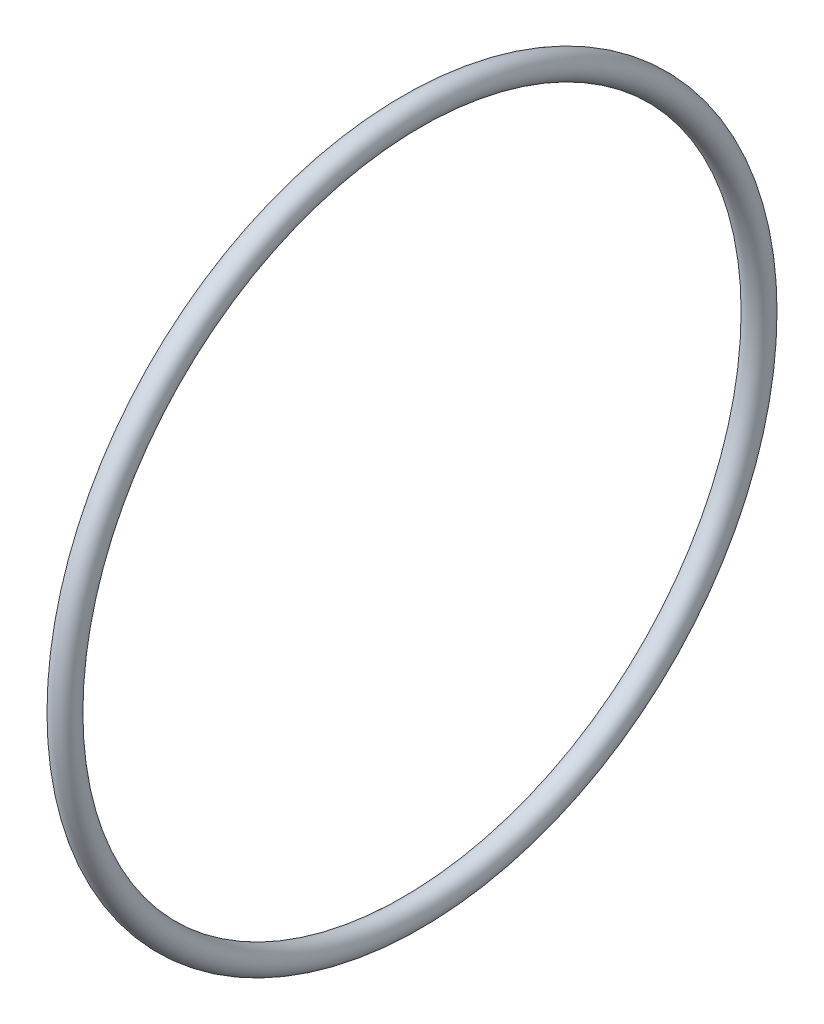
SolidWorks part; units mm, degrees
ref_plane "Front Plane" through (0, 0, 0) normal (0, 0, 1) x (1, 0, 0)
ref_plane "Top Plane" through (0, 0, 0) normal (0, 1, 0) x (1, 0, 0)
ref_plane "Right Plane" through (0, 0, 0) normal (1, 0, 0) x (0, 0, -1)
sketch "Sketch2" plane through (0, 0, 0) normal (0, 0, 1) x (1, 0, 0)
  line L0 (0, 0) -> (58.591, 0) construction
  line L2 (0, 0) -> (18.4, 0)
  line L3 (0, 0) -> (0, 2.5)
  line L4 (0, 2.5) -> (18.4, 2.5)
  line L5 (18.4, 0) -> (18.4, 2.5)
  line L6 (6.0094, 2.5) -> (6.0094, 6)
  line L11 (6.0094, 6) -> (9.9794, 6)
  line L16 (12.9794, 6) -> (12.9794, 3)
  line L17 (12.9794, 3) -> (13.6398, 3)
  line L18 (13.6398, 3) -> (13.6398, 2.5)
  line L19 (13.6398, 2.5) -> (6.0094, 2.5)
  line L22 (13.6398, 2.5) -> (16.1198, 2.5)
  line L23 (13.6398, 2.5) -> (13.6398, 4)
  line L24 (13.6398, 4) -> (16.1198, 4)
  line L25 (16.1198, 2.5) -> (16.1198, 4)
  line L27 (6.0094, 6) -> (9.9794, 6)
  line L28 (6.0094, 6) -> (6.0094, 9)
  line L29 (6.0094, 9) -> (9.9794, 9)
  line L30 (9.9794, 6) -> (9.9794, 9)
  line L31 (6.0094, 9) -> (6.0094, 8.25)
  line L32 (6.0094, 8.25) -> (5.0094, 8.25)
  line L33 (8.6609, 22.001) -> (8.6609, 12.476) construction
  line L34 (5.0094, 12.476) -> (12.3124, 12.476)
  line L35 (9.9794, 9) -> (12.3124, 9)
  line L36 (5.0094, 7.9375) -> (1.7709, 7.9375)
  line L37 (5.0094, 8.25) -> (5.0094, 12.476)
  line L38 (5.0094, 7.9375) -> (5.0094, 13.9365)
  line L39 (5.0094, 13.9365) -> (1.7709, 13.9365)
  line L40 (1.7709, 7.9375) -> (1.7709, 13.9365)
  line L41 (5.0094, 22.001) -> (12.3124, 22.001)
  line L42 (5.0094, 22.001) -> (5.0094, 30.1625)
  line L43 (5.0094, 30.1625) -> (12.3124, 30.1625)
  line L44 (12.3124, 22.001) -> (12.3124, 30.1625)
  line L49 (16.6398, 22.001) -> (16.6398, 7.5)
  line L51 (23.0198, 7.5) -> (23.0198, 6.5)
  line L54 (16.1198, 4) -> (13.6398, 4)
  line L56 (18.0398, 7.5) -> (23.0198, 7.5)
  line L57 (13.3124, 22.001) -> (16.6398, 22.001)
  line L58 (16.1198, 3.5) -> (20.0198, 3.5)
  line L59 (29.9098, 14) -> (26.9098, 11)
  line L60 (4.0094, 31.75) -> (18.0398, 31.75)
  line L61 (18.0398, 7.5) -> (23.0198, 7.5)
  line L62 (18.0398, 7.5) -> (18.0398, 12)
  line L63 (18.0398, 12) -> (23.0198, 12)
  line L64 (23.0198, 7.5) -> (23.0198, 12)
  line L65 (18.0398, 31.75) -> (18.0398, 12)
  line L66 (23.0198, 11) -> (26.9098, 11)
  line L67 (34.8098, 23) -> (31.3098, 19.5)
  line L68 (35.8098, 31) -> (38.7998, 33.99)
  line L69 (29.9098, 14) -> (29.9098, 15)
  line L70 (29.9098, 15) -> (22.9398, 15)
  line L71 (22.9398, 15) -> (21.0398, 15)
  line L72 (18.0398, 7.5) -> (16.6398, 7.5)
  line L73 (21.0398, 15) -> (21.0398, 43)
  line L74 (19.6115, 40) -> (9.6516, 40)
  line L75 (9.6516, 40) -> (4.0094, 40)
  line L76 (21.0398, 43) -> (19.6115, 43)
  line L77 (22.9398, 15) -> (29.9098, 15)
  line L78 (22.9398, 15) -> (22.9398, 21)
  line L79 (22.9398, 21) -> (29.9098, 21)
  line L80 (29.9098, 15) -> (29.9098, 21)
  line L81 (9.6516, 40) -> (19.6115, 40)
  line L82 (9.6516, 40) -> (9.6516, 50)
  line L83 (9.6516, 50) -> (19.6115, 50)
  line L84 (19.6115, 40) -> (19.6115, 50)
  line L85 (4.0094, 40) -> (4.0094, 31.75)
  line L86 (12.9794, 3) -> (12.9794, 2.5)
  line L87 (31.3098, 19.5) -> (29.9098, 19.5)
  line L88 (21.4694, 63.5) -> (21.4694, 51.308)
  line L89 (21.4694, 63.5) -> (25.9398, 63.5)
  line L90 (25.9398, 63.5) -> (25.9398, 25)
  line L91 (27.8398, 25) -> (25.9398, 25)
  line L92 (9.6516, 48) -> (8.2233, 48)
  line L93 (8.2233, 48) -> (8.2233, 53.476)
  line L94 (8.2233, 53.476) -> (19.6115, 53.476)
  line L95 (19.6115, 53.476) -> (19.6115, 50)
  line L96 (13.9174, 63.001) -> (13.9174, 53.476) construction
  line L97 (8.2233, 63.001) -> (19.6115, 63.001)
  line L98 (8.2233, 63.001) -> (8.2233, 68.2625)
  line L99 (8.2233, 68.2625) -> (19.6115, 68.2625)
  line L100 (19.6115, 63.001) -> (19.6115, 68.2625)
  line L101 (12.9794, 6) -> (11.9794, 6)
  line L102 (8.2233, 44.825) -> (4.9848, 44.825)
  line L103 (8.2233, 44.825) -> (8.2233, 54.9365)
  line L104 (8.2233, 54.9365) -> (4.9848, 54.9365)
  line L106 (9.9794, 6) -> (10.8794, 6)
  line L107 (27.8398, 25) -> (34.8098, 25)
  line L108 (34.8098, 25) -> (34.8098, 23)
  line L109 (0, 0) -> (-2, 0)
  line L110 (0, 0) -> (0, 11)
  line L111 (27.8398, 25) -> (34.8098, 25)
  line L112 (27.8398, 25) -> (27.8398, 32.5)
  line L113 (27.8398, 32.5) -> (34.8098, 32.5)
  line L114 (34.8098, 25) -> (34.8098, 32.5)
  line L115 (35.8098, 31) -> (34.8098, 31)
  line L116 (27.8398, 32.5) -> (27.8398, 64.5)
  line L117 (20.5849, 74.025) -> (6.2499, 74.025)
  line L118 (6.2499, 74.025) -> (6.2499, 76.2)
  line L119 (38.7998, 47.29) -> (30.8398, 55.25)
  line L120 (0, 11) -> (-2, 11)
  line L121 (38.7998, 43.815) -> (30.8623, 43.815)
  line L123 (-4.8152, 69.85) -> (1.5348, 76.2)
  line L124 (38.7998, 47.29) -> (38.7998, 33.99)
  line L125 (-2, 0) -> (-2, 11)
  line L126 (38.7998, 37.465) -> (30.8623, 37.465)
  line L127 (30.8623, 43.815) -> (30.8623, 37.465)
  line L128 (6.0094, 2.5) -> (6.0094, 0)
  line L129 (-0.0152, 63.5) -> (-0.0152, 30)
  line L132 (4.9848, 63.5) -> (-0.0152, 63.5)
  line L136 (-1.8152, 30) -> (-11.7752, 30)
  line L138 (-13.7752, 25.4) -> (-2, 25.4)
  line L139 (-2, 25.4) -> (-2, 11.5)
  line L140 (27.8398, 64.5) -> (20.5849, 64.5)
  line L141 (-1.8152, 30) -> (-11.7752, 30)
  line L142 (-1.8152, 30) -> (-1.8152, 39)
  line L143 (-1.8152, 39) -> (-11.7752, 39)
  line L144 (-11.7752, 30) -> (-11.7752, 39)
  line L145 (20.5849, 64.5) -> (20.5849, 74.025)
  line L146 (-12.7752, 37) -> (-12.7752, 47.29)
  line L147 (-12.7752, 37) -> (-11.7752, 37)
  line L148 (30.8398, 55.25) -> (30.8398, 76.2)
  line L149 (11.9794, 6) -> (11.9794, 5.45)
  line L154 (-2, 11.5) -> (0.5, 11.5)
  line L155 (4.9848, 60.6197) -> (24.0348, 60.6197)
  line L160 (4.9848, 60.6197) -> (4.9848, 55.8572)
  line L161 (4.9848, 55.8572) -> (24.0348, 55.8572)
  line L166 (24.0348, 60.6197) -> (24.0348, 55.8572)
  line L167 (4.9848, 60.6197) -> (24.0348, 55.8572) construction
  line L172 (4.9848, 55.8572) -> (24.0348, 60.6197) construction
  line L173 (24.0348, 62.2072) -> (25.9398, 62.2072)
  line L174 (11.9794, 5.45) -> (10.8794, 5.45)
  line L175 (10.8794, 6) -> (10.8794, 5.45)
  line L176 (24.0348, 62.2072) -> (24.0348, 54.2697)
  line L177 (24.0348, 54.2697) -> (25.9398, 54.2697)
  line L178 (25.9398, 62.2072) -> (25.9398, 54.2697)
  line L179 (24.0348, 62.2072) -> (25.9398, 54.2697) construction
  line L180 (24.0348, 54.2697) -> (25.9398, 62.2072) construction
  line L181 (3, 19.6197) -> (15.7, 19.6197)
  line L182 (3, 19.6197) -> (3, 14.8572)
  line L183 (3, 14.8572) -> (15.7, 14.8572)
  line L184 (15.7, 19.6197) -> (15.7, 14.8572)
  line L185 (3, 19.6197) -> (15.7, 14.8572) construction
  line L186 (3, 14.8572) -> (15.7, 19.6197) construction
  line L187 (15.7, 21.2072) -> (16.6398, 21.2072)
  line L188 (15.7, 21.2072) -> (15.7, 13.2697)
  line L189 (15.7, 13.2697) -> (16.6398, 13.2697)
  line L190 (16.6398, 21.2072) -> (16.6398, 13.2697)
  line L191 (15.7, 21.2072) -> (16.6398, 13.2697) construction
  line L192 (15.7, 13.2697) -> (16.6398, 21.2072) construction
  line L193 (0.5, 11.5) -> (0.5, 6.9375)
  line L194 (0.5, 6.9375) -> (1.7709, 6.9375)
  line L195 (23.0198, 6.5) -> (20.0198, 3.5)
  line L196 (4.9848, 63.5) -> (4.9848, 54.9365)
  line L197 (3, 43.825) -> (4.9848, 43.825)
  line L198 (1.7709, 6.9375) -> (1.7709, 7.9375)
  line L199 (6.0094, 0) -> (12.9794, 0)
  line L200 (12.9794, 0) -> (12.9794, 2.5)
  line L201 (18.0398, 31.75) -> (18.0398, 35.875)
  line L202 (18.0398, 35.875) -> (21.0398, 35.875)
  line L203 (30.8398, 76.2) -> (6.2499, 76.2)
  line L204 (2.8049, 69.85) -> (7.2499, 69.85) construction
  line L205 (7.2499, 67.4688) -> (26.2999, 67.4688)
  line L206 (7.2499, 74.025) -> (7.2499, 64.5)
  line L207 (7.2499, 64.5) -> (-1.8152, 64.5)
  line L208 (-1.8152, 64.5) -> (-1.8152, 39)
  line L209 (-12.7752, 47.29) -> (-4.8152, 55.25)
  line L210 (-4.8152, 55.25) -> (-4.8152, 69.85)
  line L211 (7.2499, 67.4688) -> (7.2499, 72.2312)
  line L212 (7.2499, 72.2312) -> (26.2999, 72.2313)
  line L213 (26.2999, 67.4688) -> (26.2999, 72.2313)
  line L214 (26.2999, 73.8187) -> (30.8398, 73.8187)
  line L215 (26.2999, 73.8187) -> (26.2999, 65.8813)
  line L216 (26.2999, 65.8813) -> (30.8398, 65.8813)
  line L217 (30.8398, 73.8187) -> (30.8398, 65.8813)
  line L218 (2.8049, 72.2313) -> (25.0299, 72.2313)
  line L219 (2.8049, 72.2313) -> (2.8049, 67.4687)
  line L220 (2.8049, 67.4687) -> (25.0299, 67.4687)
  line L221 (25.0299, 72.2313) -> (25.0299, 67.4687)
  line L222 (25.0299, 69.85) -> (20.5849, 69.85) construction
  line L223 (21.4694, 51.308) -> (22.9398, 51.308)
  line L224 (22.9398, 51.308) -> (22.9398, 21)
  line L225 (13.6398, 4) -> (13.6398, 12.2697)
  line L226 (13.6398, 12.2697) -> (13.3124, 12.2697)
  line L227 (13.3124, 12.2697) -> (13.3124, 22.001)
  line L228 (12.3124, 9) -> (12.3124, 12.476)
  line L229 (-1.8152, 30) -> (-0.0152, 30)
  line L230 (8.2233, 65.6317) -> (2.8049, 65.6317) construction
  line L231 (19.6115, 65.6317) -> (25.0299, 65.6317) construction
  line L232 (1.5348, 76.2) -> (6.2499, 76.2)
  line L233 (-11.7752, 30) -> (-13.7752, 30)
  line L234 (-13.7752, 30) -> (-13.7752, 25.4)
  line L235 (3, 13.9365) -> (3, 43.825)
  line L236 (4.9848, 54.9365) -> (4.9848, 44.825)
  line L237 (4.9848, 43.825) -> (4.9848, 44.825)
  circle A0 centre (26.8898, 25.95) radius 0.95
  circle A1 centre (21.9898, 15.95) radius 0.95
  circle A2 centre (17.3398, 8.2) radius 0.7
  circle A3 centre (10.4294, 6.45) radius 0.45
  circle A4 centre (-0.9152, 30.9) radius 0.9
  point P7 (24.9873, 58.2385)
  point P131 (16.1699, 17.2385)
  point P135 (14.5098, 58.2385)
  point P146 (9.35, 17.2385)
sketch "Sketch3" plane through (0, 0, 0) normal (0, 0, 1) x (1, 0, 0)
  circle A0 centre (26.8898, 25.95) radius 0.95 construction
  circle A1 centre (26.8898, 25.95) radius 0.95
revolve "Revolve1" add sketch "Sketch3" angle 360 about L0
